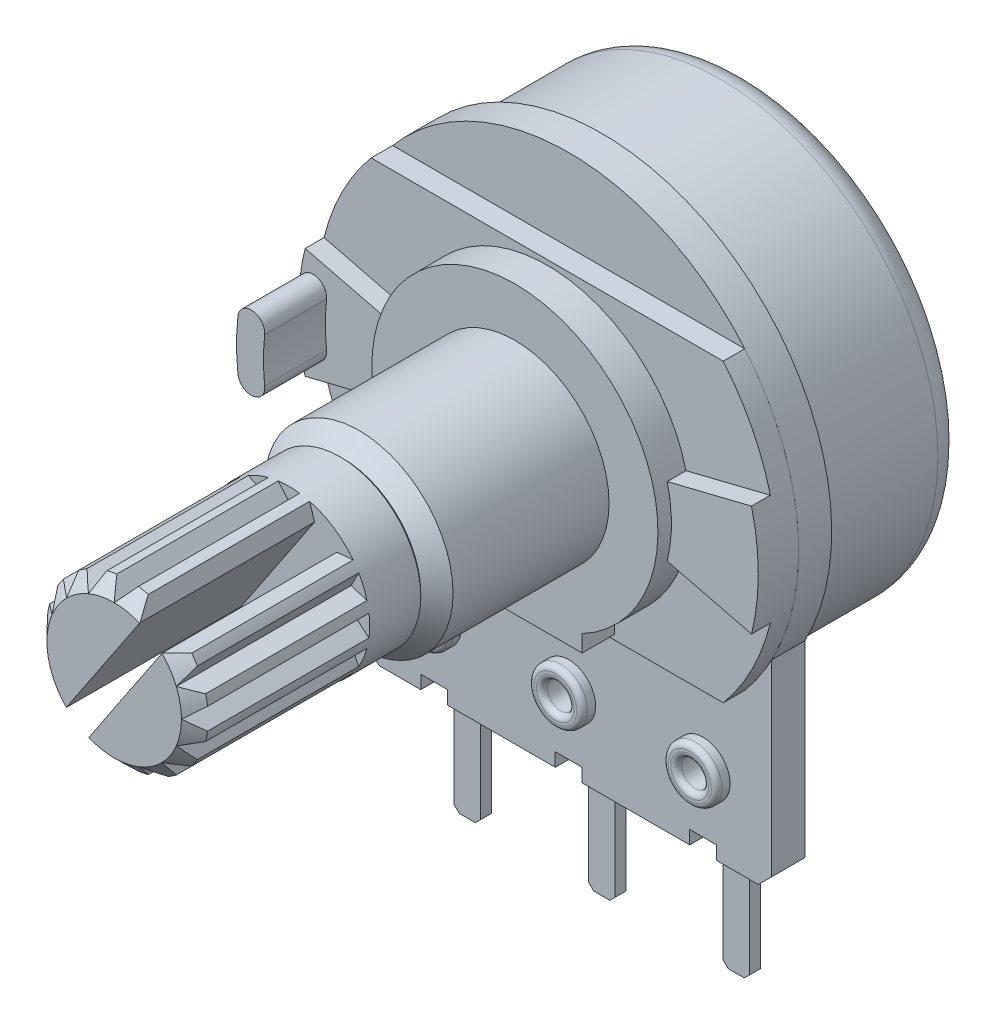
SolidWorks part; units mm, degrees
ref_plane "Front Plane" through (0, 0, 0) normal (0, 0, 1) x (1, 0, 0)
ref_plane "Top Plane" through (0, 0, 0) normal (0, 1, 0) x (1, 0, 0)
ref_plane "Right Plane" through (0, 0, 0) normal (1, 0, 0) x (0, 0, -1)
sketch "Sketch1" plane through (0, 0, 0) normal (0, 0, 1) x (1, 0, 0)
  circle A0 centre (0, 0) radius 8.1
  dimension "D1" = 16.2
extrude "Boss-Extrude1" add sketch "Sketch1" along normal blind 5.4
fillet "Fillet1" radius 1 1 edges at (8.1, 0, 0)
shell "Shell1" thickness 0.3
sketch "Sketch2" plane through (0, 0, 5.4) normal (0, 0, 1) x (1, 0, 0)
  line L2 (-7.55, -4.0125) -> (-7.55, -11.5)
  line L3 (-7.55, -11.5) -> (7.55, -11.5)
  line L4 (7.55, -4.0125) -> (7.55, -11.5)
  arc A0 (7.55, -4.0125) -> (-7.55, -4.0125) centre (0, 0) ccw
  dimension "D4" = 8.55
  dimension "D1" = 11.5
  dimension "D2" = 7.55
  dimension "D3" = 7.55
extrude "Boss-Extrude2" add sketch "Sketch2" along normal blind 1.23 separate body
chamfer "Chamfer1" distance 0.5 angle 45 2 edges at (7.55, -11.5, 6.015) (-7.55, -11.5, 6.015)
sketch "Sketch3" plane through (0, 0, 6.63) normal (0, 0, 1) x (1, 0, 0)
  line L0 (-2.0533, 0) -> (3.7862, 0) construction
  line L1 (-6.5462, 5.5) -> (6.5462, 5.5)
  line L3 (-6.5462, -5.5) -> (6.5462, -5.5)
  arc A0 (-6.5462, 5.5) -> (-6.5462, -5.5) centre (0, 0) ccw
  arc A1 (6.5462, -5.5) -> (6.5462, 5.5) centre (0, 0) ccw
  point P0 (0, 0)
  dimension "D1" = 8.55
  dimension "D2" = 11
extrude "Boss-Extrude3" add sketch "Sketch3" along normal blind 0.8 separate body
sketch "Sketch4" plane through (0, 0, 7.43) normal (0, 0, 1) x (1, 0, 0)
  line L1 (2.5, -4.696) -> (2.5, -5.32)
  line L2 (0, 2.957) -> (0, -9.2499) construction
  line L3 (-2.5, -4.696) -> (-2.5, -5.32)
  line L4 (-2.5, -5.32) -> (2.5, -5.32)
  arc A0 (2.5, -4.696) -> (-2.5, -4.696) centre (0, 0) ccw
  arc A1 (-2.5, -4.696) -> (2.5, -4.696) centre (0, 0) ccw construction
  dimension "D2" = 10.64
  dimension "D1" = 5
extrude "Boss-Extrude4" add sketch "Sketch4" along normal blind 1.2 contours L4 L1 A0 L3
sketch "Esquisse1" plane through (0, 0, 7.43) normal (0, 0, 1) x (1, 0, 0)
  line L0 (-5.1633, 1.2818) -> (-8.2981, 2.06)
  line L1 (-8.2981, -2.06) -> (-5.1633, -1.2818)
  line L2 (-8.2981, 2.06) -> (8.2981, -2.06) construction
  line L3 (-8.2981, -2.06) -> (8.2981, 2.06) construction
  line L4 (5.1633, 1.2818) -> (8.2981, 2.06)
  line L5 (8.2981, -2.06) -> (5.1633, -1.2818)
  line L6 (-2.3876, 0) -> (2.8565, 0) construction
  arc A0 (2.5, -4.696) -> (-2.5, -4.696) centre (0, 0) ccw construction
  arc A1 (-6.5462, 5.5) -> (-6.5462, -5.5) centre (0, 0) ccw construction
  arc A2 (-8.2981, 2.06) -> (-8.2981, -2.06) centre (0, 0) ccw
  arc A3 (-5.1633, -1.2818) -> (-5.1633, 1.2818) centre (0, 0) cw
  arc A4 (6.5462, -5.5) -> (6.5462, 5.5) centre (0, 0) ccw construction
  arc A5 (8.2981, 2.06) -> (8.2981, -2.06) centre (0, 0) cw
  arc A6 (5.1633, -1.2818) -> (5.1633, 1.2818) centre (0, 0) ccw
  dimension "D1" = 4.12
extrude "Boss.-Extru.1" add sketch "Esquisse1" along normal blind 0.7
sketch "Esquisse2" plane through (0, 0, 8.13) normal (0, 0, 1) x (1, 0, 0)
  line L0 (0, 0) -> (-11.6632, 0) construction
  arc A0 (-8.4993, 0.9293) -> (-8.4993, -0.9293) centre (0, 0) ccw
  arc A1 (-8.2981, 2.06) -> (-8.2981, -2.06) centre (0, 0) ccw construction
  arc A2 (-7.5053, 0.8207) -> (-7.5053, -0.8207) centre (0, 0) ccw
  arc A3 (-8.4993, 0.9293) -> (-7.5053, 0.8207) centre (-8.0023, 0.875) cw
  arc A4 (-8.4993, -0.9293) -> (-7.5053, -0.8207) centre (-8.0023, -0.875) ccw
  dimension "D2" = 2.75
  dimension "D1" = 1
extrude "Boss.-Extru.2" add sketch "Esquisse2" along normal blind 2.3
sketch "Sketch5" plane through (0, 0, 8.63) normal (0, 0, 1) x (1, 0, 0)
  circle A0 centre (0, 0) radius 3.5
  dimension "D1" = 7
extrude "Boss-Extrude5" add sketch "Sketch5" along normal blind 6.4
sketch "Sketch6" plane through (0, 0, 15.03) normal (0, 0, 1) x (1, 0, 0)
  circle A0 centre (0, 0) radius 2.3
  dimension "D1" = 4.6
extrude "Cut-Extrude1" cut sketch "Sketch6" against normal blind 6
sketch "Sketch7" plane through (0, 0, 8.63) normal (0, 0, 1) x (1, 0, 0)
  circle A0 centre (0, 0) radius 2.25
  dimension "D1" = 4.5
extrude "Boss-Extrude6" add sketch "Sketch7" along normal blind 6.2
chamfer "Chamfer2" distance 0.6 angle 45 1 edges at (3.5, 0, 15.03)
sketch "Sketch9" plane through (0, 0, 15.03) normal (0, 0, 1) x (1, 0, 0)
  circle A0 centre (0, 0) radius 2.75
  dimension "D1" = 5.5
extrude "Boss-Extrude8" add sketch "Sketch9" along normal blind 0.1
sketch "Sketch10" plane through (0, 0, 15.13) normal (0, 0, 1) x (1, 0, 0)
  circle A0 centre (0, 0) radius 3
  dimension "D1" = 6
extrude "Boss-Extrude9" add sketch "Sketch10" along normal blind 8.4
chamfer "Chamfer3" distance 0.5 angle 45 1 edges at (3, 0, 23.53)
sketch "Sketch12" plane through (0, 0, 23.53) normal (0, 0, 1) x (1, 0, 0)
  line L0 (0, 3) -> (0, -3) construction
  line L1 (-0.4, 2.9732) -> (0, 2.5)
  line L2 (0, 2.5) -> (0.4, 2.9732)
  circle A0 centre (0, 0) radius 3 construction
  arc A2 (0.4, 2.9732) -> (-0.4, 2.9732) centre (0, 0) ccw
  dimension "D1" = 0.4
  dimension "D2" = 0.4
  dimension "D3" = 0.5
extrude "Cut-Extrude3" cut sketch "Sketch12" against normal blind 6.5
pattern_circular "CirPattern1" count 16 over 360 about axis through (0, 0, 0) along (0, 0, 1) of "Cut-Extrude3"
sketch "Sketch13" plane through (0, 0, 6.63) normal (0, 0, 1) x (1, 0, 0)
  line L0 (-7.55, -8.782) -> (7.55, -8.782) construction
  line L1 (-7.55, -4.0125) -> (-7.55, -11) construction
  line L2 (7.55, -4.0125) -> (7.55, -11) construction
sketch "Sketch14" plane through (0, 0, 6.63) normal (0, 0, 1) x (1, 0, 0)
  line L0 (-7.55, -8.782) -> (7.55, -8.782) construction
  circle A0 centre (-5, -8.782) radius 1
  circle A1 centre (0, -8.782) radius 1
  circle A2 centre (5, -8.782) radius 1
  dimension "D1" = 2
  dimension "D2" = 5
  dimension "D3" = 5
extrude "Boss-Extrude10" add sketch "Sketch14" along normal blind 0.5 separate body
sketch "Sketch15" plane through (0, 0, 6.63) normal (0, 0, 1) x (1, 0, 0)
  circle A0 centre (-5, -8.782) radius 0.75
  circle A1 centre (0, -8.782) radius 0.75
  circle A2 centre (5, -8.782) radius 0.75
  dimension "D1" = 1.5
extrude "Cut-Extrude5" cut sketch "Sketch15" against normal through all
sketch "Esquisse3" plane through (0, 0, 6.63) normal (0, 0, -1) x (-1, 0, 0)
  circle A0 centre (5, -8.782) radius 0.725
  circle A1 centre (0, -8.782) radius 0.725
  circle A2 centre (-5, -8.782) radius 0.725
  dimension "D1" = 1.45
extrude "Boss.-Extru.3" add sketch "Esquisse3" along normal up to surface (1.23 mm away) up to face at (5.75, -8.782, 5.4)
sketch "Esquisse4" plane through (0, 0, 7.13) normal (0, 0, 1) x (1, 0, 0)
  circle A0 centre (-5, -8.782) radius 0.5
  circle A1 centre (0, -8.782) radius 0.5
  circle A2 centre (5, -8.782) radius 0.5
  dimension "D1" = 1
extrude "Enlèv. mat.-Extru.1" cut sketch "Esquisse4" against normal up to surface (1.73 mm away) up to face at (-4.275, -8.782, 5.4)
fillet "Fillet3" radius 0.2 2 edges at (-4, -8.782, 7.13) (-4.5, -8.782, 7.13)
fillet "Congé1" radius 0.2 2 edges at (0.5, -8.782, 7.13) (1, -8.782, 7.13)
fillet "Congé2" radius 0.2 2 edges at (5.5, -8.782, 7.13) (6, -8.782, 7.13)
sketch "Sketch16" plane through (0, 0, 6.63) normal (0, 0, 1) x (1, 0, 0)
  line L0 (-5, -8.782) -> (-5, -11.5) construction
  line L1 (-7.05, -11.5) -> (7.05, -11.5) construction
  line L2 (0, -8.782) -> (0, -11.5) construction
  line L3 (-7.55, -8.782) -> (7.55, -8.782) construction
  line L4 (5, -8.782) -> (5, -11.5) construction
  line L6 (-5.5, -11) -> (-4.5, -11)
  line L7 (-5.5, -11) -> (-5.5, -12)
  line L8 (-5.5, -12) -> (-4.5, -12)
  line L9 (-4.5, -11) -> (-4.5, -12)
  line L10 (-5.5, -11) -> (-4.5, -12) construction
  line L11 (-5.5, -12) -> (-4.5, -11) construction
  line L12 (-0.5, -11) -> (0.5, -11)
  line L13 (-0.5, -11) -> (-0.5, -12)
  line L14 (-0.5, -12) -> (0.5, -12)
  line L15 (0.5, -11) -> (0.5, -12)
  line L16 (-0.5, -11) -> (0.5, -12) construction
  line L17 (-0.5, -12) -> (0.5, -11) construction
  line L18 (4.5, -11) -> (5.5, -11)
  line L19 (4.5, -11) -> (4.5, -12)
  line L20 (4.5, -12) -> (5.5, -12)
  line L21 (5.5, -11) -> (5.5, -12)
  line L22 (4.5, -11) -> (5.5, -12) construction
  line L23 (4.5, -12) -> (5.5, -11) construction
  dimension "D1" = 1
  dimension "D2" = 0.5
extrude "Cut-Extrude6" cut sketch "Sketch16" against normal up to next (1.23 mm away)
sketch "Sketch18" plane through (0, -11.5, 0) normal (0, -1, 0) x (1, 0, 0)
  line L1 (-6.275, 5.4) -> (6.275, 5.4)
  line L2 (-6.275, 5.4) -> (-6.275, 4.4)
  line L3 (-6.275, 4.4) -> (6.275, 4.4)
  line L4 (6.275, 5.4) -> (6.275, 4.4)
  line L6 (-7.05, 5.4) -> (-5.5, 5.4) construction
  line L7 (8.1, 5.4) -> (-8.1, 5.4) construction
  line L8 (5.5, 5.4) -> (7.05, 5.4) construction
  dimension "D1" = 1
extrude "Cut-Extrude7" cut sketch "Sketch18" against normal blind 10
sketch "Sketch24" plane through (0, 0, 5.4) normal (0, 0, -1) x (-1, 0, 0)
  line L0 (7.55, -8.782) -> (-7.55, -8.782) construction
  line L1 (-5.75, -5.564) -> (-4.25, -5.564)
  line L2 (-5.75, -5.564) -> (-5.75, -12)
  line L3 (-5.75, -12) -> (-4.25, -12)
  line L4 (-4.25, -5.564) -> (-4.25, -12)
  line L5 (-5.75, -5.564) -> (-4.25, -12) construction
  line L6 (-5.75, -12) -> (-4.25, -5.564) construction
  line L7 (-0.75, -5.564) -> (0.75, -5.564)
  line L8 (-0.75, -5.564) -> (-0.75, -12)
  line L9 (-0.75, -12) -> (0.75, -12)
  line L10 (0.75, -5.564) -> (0.75, -12)
  line L11 (-0.75, -5.564) -> (0.75, -12) construction
  line L12 (-0.75, -12) -> (0.75, -5.564) construction
  line L13 (-5.5, -11.5) -> (-7.05, -11.5) construction
  line L14 (4.25, -5.564) -> (5.75, -5.564)
  line L15 (4.25, -5.564) -> (4.25, -12)
  line L16 (4.25, -12) -> (5.75, -12)
  line L17 (5.75, -5.564) -> (5.75, -12)
  line L18 (4.25, -5.564) -> (5.75, -12) construction
  line L19 (4.25, -12) -> (5.75, -5.564) construction
  point P0 (-5, -8.782)
  point P6 (0, -8.782)
  point P13 (5, -8.782)
  dimension "D1" = 1.5
  dimension "D2" = 0.5
extrude "Boss-Extrude18" add sketch "Sketch24" along normal blind 0.4 separate body
sketch "Sketch25" plane through (0, -12, 0) normal (0, -1, 0) x (1, 0, 0)
  line L0 (-5, 5.4) -> (-5, 5) construction
  line L1 (-4.25, 5.4) -> (-5.75, 5.4) construction
  line L2 (-4.25, 5) -> (-5.75, 5) construction
  line L3 (0, 4.9) -> (0, 5.5) construction
  line L5 (5, 5.4) -> (5, 5) construction
  line L6 (4.5, 5.4) -> (5.5, 5.4) construction
  line L7 (5.75, 5) -> (4.25, 5) construction
  line L8 (0.75, 5) -> (-0.75, 5) construction
  line L9 (-5.5, 5.4) -> (-4.5, 5.4)
  line L10 (-5.5, 5.4) -> (-5.5, 5)
  line L11 (-5.5, 5) -> (-4.5, 5)
  line L12 (-4.5, 5.4) -> (-4.5, 5)
  line L13 (-5.5, 5.4) -> (-4.5, 5) construction
  line L14 (-5.5, 5) -> (-4.5, 5.4) construction
  line L15 (-0.5, 5.4) -> (0.5, 5.4)
  line L16 (-0.5, 5.4) -> (-0.5, 5)
  line L17 (-0.5, 5) -> (0.5, 5)
  line L18 (0.5, 5.4) -> (0.5, 5)
  line L19 (-0.5, 5.4) -> (0.5, 5) construction
  line L20 (-0.5, 5) -> (0.5, 5.4) construction
  line L21 (-0.75, 5) -> (-0.75, 5.4) construction
  line L22 (4.5, 5.4) -> (5.5, 5.4)
  line L23 (4.5, 5.4) -> (4.5, 5)
  line L24 (4.5, 5) -> (5.5, 5)
  line L25 (5.5, 5.4) -> (5.5, 5)
  line L26 (4.5, 5.4) -> (5.5, 5) construction
  line L27 (4.5, 5) -> (5.5, 5.4) construction
  line L28 (0.75, 5) -> (0.75, 5.4) construction
  line L29 (0.75, 5.4) -> (-0.75, 5.4) construction
  point P16 (-5, 5.2)
  point P21 (0, 5.2)
  point P28 (5, 5.2)
  dimension "D1" = 1
extrude "Boss-Extrude19" add sketch "Sketch25" along normal blind 4
chamfer "Chamfer4" distance 0.2 angle 45 2 edges at (4.5, -16, 5.2) (5.5, -16, 5.2)
chamfer "Chamfer5" distance 0.2 angle 45 2 edges at (-0.5, -16, 5.2) (0.5, -16, 5.2)
chamfer "Chamfer6" distance 0.2 angle 45 1 edges at (-4.5, -16, 5.2)
sketch "Sketch26" plane through (0, 0, 5.4) normal (0, 0, 1) x (1, 0, 0)
  line L0 (-7.55, -8.782) -> (7.55, -8.782) construction
  circle A0 centre (-5, -8.782) radius 0.5
  circle A1 centre (0, -8.782) radius 0.5
  circle A2 centre (5, -8.782) radius 0.5
extrude "Cut-Extrude9" cut sketch "Sketch26" against normal up to surface (0.4 mm away) up to face at (5.025, -12.6528, 5)
sketch "Sketch28" plane through (0, 0, 23.53) normal (0, 0, 1) x (1, 0, 0)
  line L0 (-1.6667, -2.4944) -> (1.6667, 2.4944) construction
  line L1 (-1.251, -2.7722) -> (2.0824, 2.2166)
  line L2 (2.0824, 2.2166) -> (1.251, 2.7722)
  line L3 (1.251, 2.7722) -> (-2.0824, -2.2166)
  line L4 (-2.0824, -2.2166) -> (-1.251, -2.7722)
  arc A0 (-1.8195, -2.3852) -> (-1.5074, -2.5938) centre (0, 0) ccw construction
  dimension "D1" = 1
  dimension "D2" = 1
extrude "Cut-Extrude11" cut sketch "Sketch28" against normal blind 6.5
